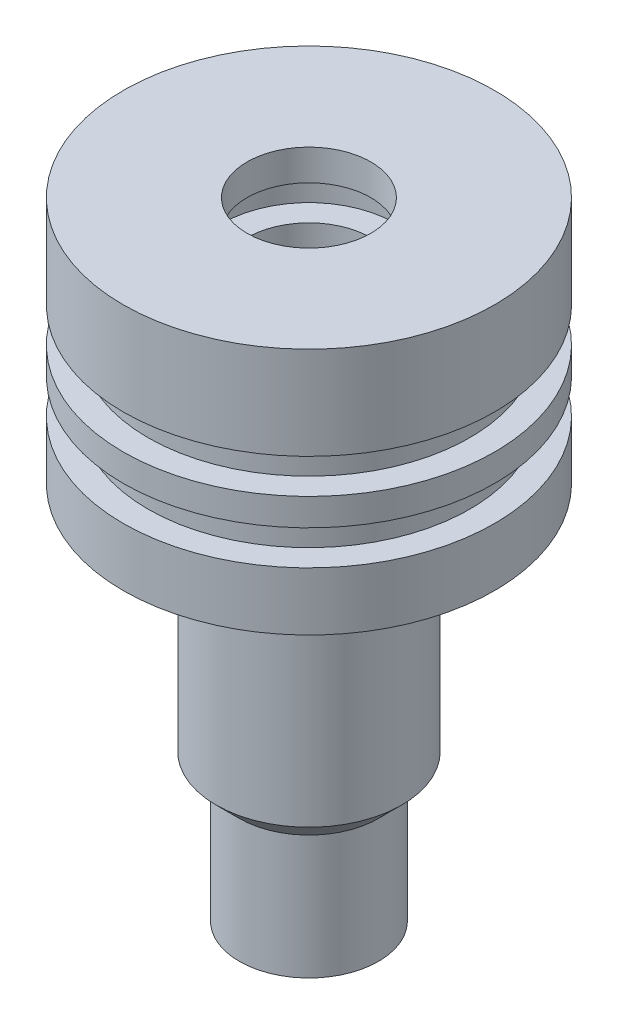
SolidWorks part; units mm, degrees
ref_plane "Front Plane" through (0, 0, 0) normal (0, 0, 1) x (1, 0, 0)
ref_plane "Top Plane" through (0, 0, 0) normal (0, 1, 0) x (1, 0, 0)
ref_plane "Right Plane" through (0, 0, 0) normal (1, 0, 0) x (0, 0, -1)
sketch "Sketch1" plane through (0, 0, 0) normal (0, 0, 1) x (1, 0, 0)
  line L0 (-6.35, -13.081) -> (-6.35, -64.2938)
  line L1 (-6.35, -64.2938) -> (-7.1437, -64.2938)
  line L2 (-7.1437, -64.2938) -> (-7.1437, -51.5938)
  line L3 (-7.1437, -51.5938) -> (-9.525, -49.2125)
  line L4 (-7.1437, -51.5938) -> (-10.9407, -51.5938) construction
  line L5 (-9.525, -49.2125) -> (-9.525, -25.4)
  line L6 (-9.525, -25.4) -> (-19.05, -25.4)
  line L7 (-19.05, -25.4) -> (-19.05, -19.431)
  line L8 (-19.05, 0) -> (-6.35, 0)
  line L9 (-6.35, -13.081) -> (-8.89, -13.081)
  line L10 (-8.89, -13.081) -> (-8.89, -9.525)
  line L11 (-8.89, -9.525) -> (-6.35, -9.525)
  line L12 (-6.35, -9.525) -> (-6.35, -6.731)
  line L13 (-6.35, -6.731) -> (-8.89, -6.731)
  line L14 (-8.89, -6.731) -> (-8.89, -3.175)
  line L15 (-8.89, -3.175) -> (-6.35, -3.175)
  line L16 (-6.35, -3.175) -> (-6.35, 0)
  line L17 (-19.05, -19.431) -> (-16.51, -19.431)
  line L18 (-16.51, -19.431) -> (-16.51, -15.875)
  line L19 (-16.51, -15.875) -> (-19.05, -15.875)
  line L20 (-19.05, -15.875) -> (-19.05, -13.081)
  line L21 (-19.05, -13.081) -> (-16.51, -13.081)
  line L22 (-16.51, -13.081) -> (-16.51, -9.525)
  line L23 (-16.51, -9.525) -> (-19.05, -9.525)
  line L24 (-19.05, -9.525) -> (-19.05, 0)
  line L25 (0, 0) -> (0, -107.0078) construction
  dimension "D1" = 0.7938
  dimension "D2" = 45
  dimension "D3" = 6.35
  dimension "D4" = 12.7
  dimension "D5" = 3.175
  dimension "D6" = 23.8125
  dimension "D7" = 25.4
  dimension "D8" = 19.05
  dimension "D9" = 3.175
  dimension "D10" = 3.556
  dimension "D11" = 2.54
  dimension "D12" = 3.556
  dimension "D13" = 2.54
  dimension "D15" = 2.54
  dimension "D16" = 3.556
  dimension "D17" = 9.525
  dimension "D14" = 6.35
  dimension "D18" = 2.54
  dimension "D19" = 3.556
  dimension "D20" = 6.35
revolve "Revolve1" add sketch "Sketch1" angle 360 about L25
equation "\"D12@Sketch1\"=\"D10@Sketch1\""
equation "\"D13@Sketch1\"=\"D11@Sketch1\""
equation "\"D19@Sketch1\"=\"D16@Sketch1\""
equation "\"D18@Sketch1\"=\"D15@Sketch1\""
